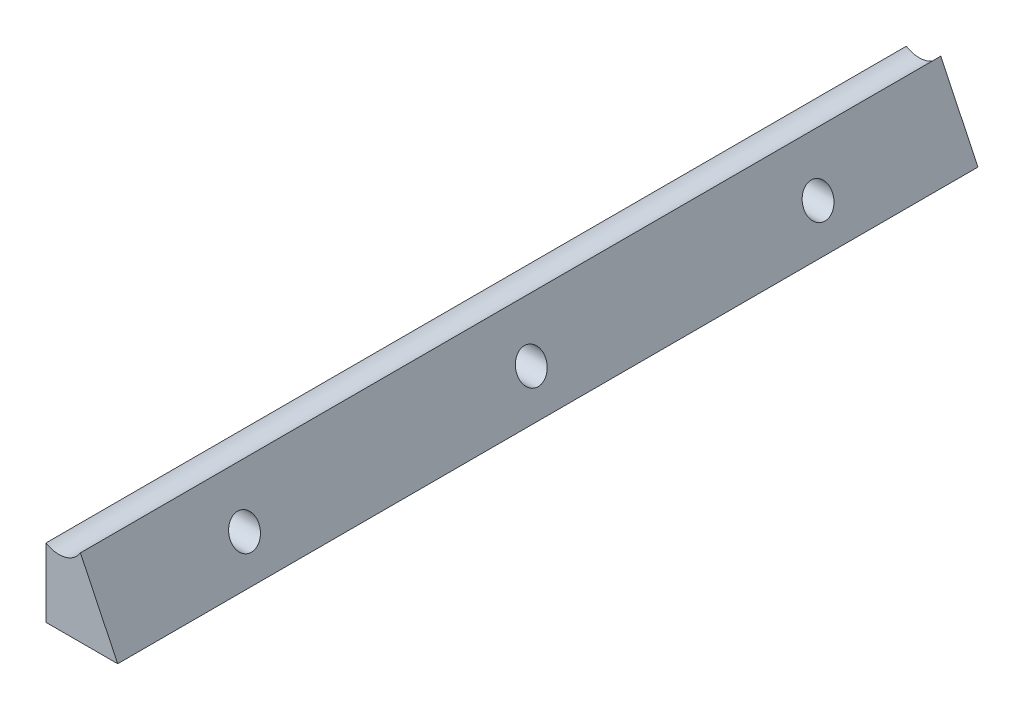
SolidWorks part; units mm, degrees
ref_plane "Plan de face" through (0, 0, 0) normal (0, 0, 1) x (1, 0, 0)
ref_plane "Plan de dessus" through (0, 0, 0) normal (0, 1, 0) x (1, 0, 0)
ref_plane "Plan de droite" through (0, 0, 0) normal (1, 0, 0) x (0, 0, -1)
sketch "Esquisse1" plane through (0, 0, 0) normal (0, 0, 1) x (1, 0, 0)
  line L0 (0, 0) -> (12.5, 0)
  line L1 (0, 0) -> (0, 12)
  line L2 (6, 13.5) -> (12.5, 0)
  arc A0 (0, 12) -> (6, 13.5) centre (2.25, 15.75) ccw
  point P3 (6, 13.5)
  dimension "D1" = 12.5
  dimension "D2" = 12
  dimension "D3" = 13.5
  dimension "D4" = 6
extrude "Boss.-Extru.1" add sketch "Esquisse1" along normal blind 150
sketch "Esquisse2" plane through (0, 0, 0) normal (-1, 0, 0) x (0, 0, 1)
  line L0 (0, 6) -> (150, 6)
  line L1 (0, 12) -> (0, 0) construction
  line L2 (150, 12) -> (150, 0) construction
  point P6 (25, 6)
  point P7 (75, 6)
  point P8 (125, 6)
  dimension "D1" = 25
  dimension "D2" = 25
hole_wizard "Trou taraudé M63" positions "Esquisse3D2" profile "Esquisse6" tap size "M6" standard "ISO" end condition through all
sketch3d "Esquisse3D2"
  point P0 (0, 6, 25)
  point P3 (0, 6, 75)
  point P6 (0, 6, 125)
sketch "Esquisse6" plane through (0, 6, 25) normal (0, 1, 0) x (0, 0, 1)
  line L0 (0, 0) -> (0, 12.5)
  line L1 (0, 12.5) -> (2.5, 12.5)
  line L2 (2.5, 12.5) -> (2.5, 0)
  line L5 (2.5, 0) -> (0, 0)
  line L11 (0, -6.35) -> (0, 107.95) construction
  dimension "Diamètre du trou pour taraudage jusqu'au prochain" = 5
  dimension "Profondeur du trou pour taraudage jusqu'au prochain" = 12.5
cosmetic thread "Filetage de perçage7" parameters "D2"=6
cosmetic thread "Filetage de perçage8" parameters "D2"=6
cosmetic thread "Filetage de perçage9" parameters "D2"=6
